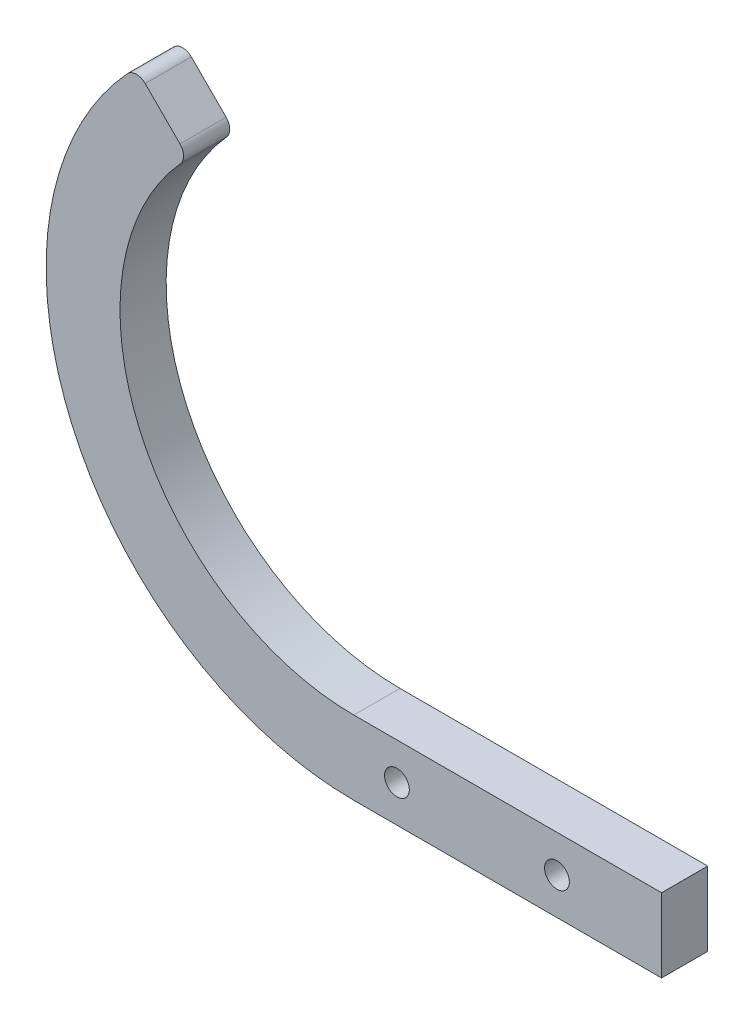
SolidWorks part; units mm, degrees
ref_plane "Front Plane" through (0, 0, 0) normal (0, 0, 1) x (1, 0, 0)
ref_plane "Top Plane" through (0, 0, 0) normal (0, 1, 0) x (1, 0, 0)
ref_plane "Right Plane" through (0, 0, 0) normal (1, 0, 0) x (0, 0, -1)
sketch "Sketch2" plane through (0, 0, 0) normal (0, 0, 1) x (1, 0, 0)
  line L0 (0, -63.5) -> (63.5, -63.5)
  line L1 (0, -48.26) -> (63.5, -48.26)
  line L2 (63.5, -48.26) -> (63.5, -63.5)
  line L3 (-43.0678, 43.0678) -> (-35.8761, 35.8761)
  arc A0 (-46.7332, 42.9914) -> (0, -63.5) centre (0, 0) ccw
  arc A1 (-35.7885, 32.376) -> (0, -48.26) centre (0, 0) ccw
  arc A2 (-41.3803, 48.1655) -> (0, -63.5) centre (0, 0) ccw construction
  arc A3 (-43.0678, 43.0678) -> (-46.7332, 42.9914) centre (-44.8638, 41.2717) ccw
  arc A4 (-31.449, 36.6058) -> (0, -48.26) centre (0, 0) ccw construction
  arc A5 (-35.7885, 32.376) -> (-35.8761, 35.8761) centre (-37.6721, 34.08) ccw
  dimension "D1" = 63.5
  dimension "D4" = 2.54
  dimension "D5" = 2.54
  dimension "D3" = 63.5
  dimension "D6" = 45
  dimension "D2" = 15.24
extrude "Boss-Extrude1" add sketch "Sketch2" along normal blind 9.525 contours A0 L0 L2 L1 A1 A5 L3 A3
sketch "Sketch3" plane through (0, 0, 0) normal (0, 0, 1) x (1, 0, 0)
  line L0 (0, -55.88) -> (63.5, -55.88) construction
  line L1 (63.5, -63.5) -> (0, -63.5)
  line L2 (63.5, -63.5) -> (63.5, -48.26)
  line L3 (63.5, -48.26) -> (0, -48.26)
  line L4 (0, -63.5) -> (0, -48.26)
  circle A0 centre (8.89, -55.88) radius 2.921
  circle A1 centre (41.91, -55.88) radius 2.921
  dimension "D5" = 5.842
  dimension "D6" = 5.842
  dimension "D1" = 7.62
  dimension "D3" = 33.02
  dimension "D4" = 8.89
hole_wizard "1/4-20 Tapped Hole1" positions "Sketch4" profile "Sketch5" tap size "1/4-20" standard "ANSI Inch" end condition through all
sketch "Sketch4" plane through (0, 0, 9.525) normal (0, 0, 1) x (1, 0, 0)
  point P0 (8.89, -55.88)
  point P3 (41.91, -55.88)
sketch "Sketch5" plane through (8.89, -55.88, 9.525) normal (1, 0, 0) x (0, -1, 0)
  line L0 (0, 0) -> (0, 9.525)
  line L1 (0, 9.525) -> (2.5527, 9.525)
  line L2 (2.5527, 9.525) -> (2.5527, 0)
  line L5 (2.5527, 0) -> (0, 0)
  line L11 (0, -6.35) -> (0, 107.95) construction
  dimension "Thru Tap Drill Dia." = 5.1054
  dimension "Thru Tap Drill Depth" = 9.525
cosmetic thread "Hole Thread1" parameters "D2"=6.35
cosmetic thread "Hole Thread2" parameters "D2"=6.35
